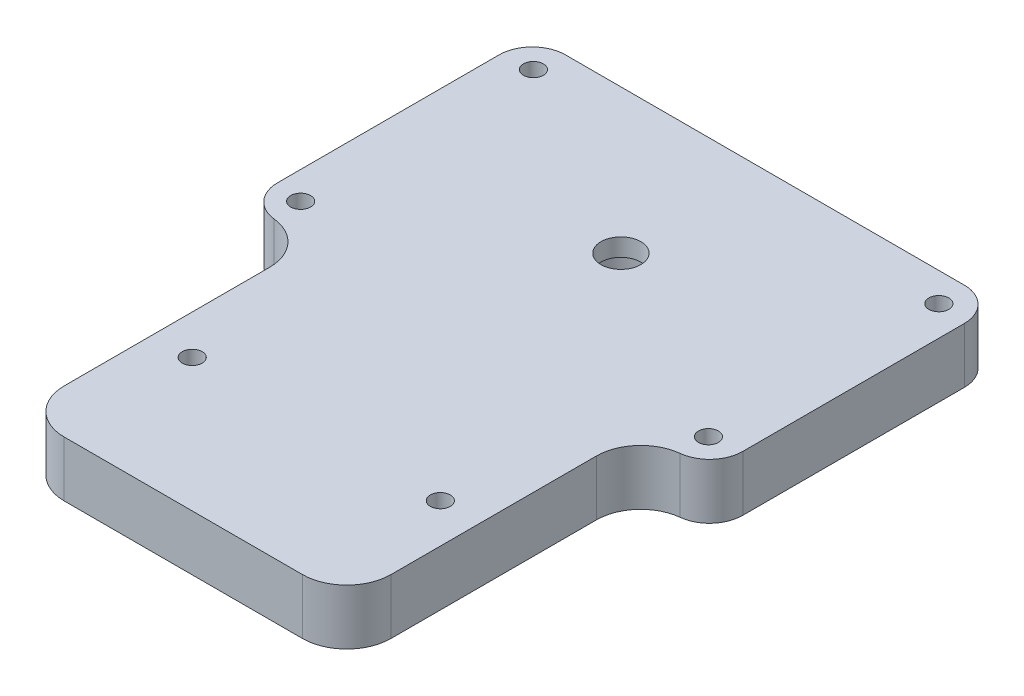
SolidWorks part; units mm, degrees
ref_plane "Front Plane" through (0, 0, 0) normal (0, 0, 1) x (1, 0, 0)
ref_plane "Top Plane" through (0, 0, 0) normal (0, 1, 0) x (1, 0, 0)
ref_plane "Right Plane" through (0, 0, 0) normal (1, 0, 0) x (0, 0, -1)
sketch "Sketch1" plane through (0, 0, 0) normal (0, 1, 0) x (1, 0, 0)
  line L0 (-20.8014, 12.877) -> (26.67, -16.51) construction
  line L1 (-22.86, 16.51) -> (22.86, 16.51)
  line L2 (-26.67, 12.7) -> (-26.67, -12.7)
  line L3 (-22.86, -16.51) -> (-18.7325, -16.51)
  line L4 (26.67, 12.7) -> (26.67, -12.7)
  line L5 (-26.67, 16.51) -> (-22.7451, 14.0803) construction
  line L6 (-26.67, -16.51) -> (26.67, 16.51) construction
  line L7 (18.7325, -16.51) -> (22.86, -16.51)
  line L9 (18.7325, -16.51) -> (18.7325, -50.165)
  line L10 (18.7325, -50.165) -> (-18.7325, -50.165)
  line L11 (-18.7325, -16.51) -> (-18.7325, -50.165)
  circle A0 centre (-23.241, 13.208) radius 1.143
  circle A1 centre (23.241, 13.208) radius 1.143
  circle A2 centre (23.241, -13.208) radius 1.143
  circle A3 centre (-23.5075, -13.208) radius 1.143
  arc A4 (-22.86, 16.51) -> (-26.67, 12.7) centre (-22.86, 12.7) ccw
  arc A5 (-26.67, -12.7) -> (-22.86, -16.51) centre (-22.86, -12.7) ccw
  arc A6 (22.86, -16.51) -> (26.67, -12.7) centre (22.86, -12.7) ccw
  arc A7 (22.86, 16.51) -> (26.67, 12.7) centre (22.86, 12.7) cw
  circle A8 centre (14.224, -34.925) radius 1.143
  circle A9 centre (-14.224, -34.925) radius 1.143
  point P0 (0, 0)
  point P14 (-24.384, 13.208)
  point P18 (24.384, 14.35)
  point P34 (0, -50.165)
  point P39 (13.081, -34.925)
  point P40 (-13.081, -34.925)
  point P41 (14.224, -36.068)
  dimension "D3" = 2.286
  dimension "D5" = 46.482
  dimension "D7" = 26.416
  dimension "D8" = 13.208
  dimension "D9" = 3.81
  dimension "D12" = 2.286
  dimension "D13" = 28.448
  dimension "D14" = 14.224
  dimension "D1" = 53.34
  dimension "D2" = 33.02
  dimension "D4" = 48.768
  dimension "D6" = 23.241
  dimension "D10" = 37.465
  dimension "D11" = 33.655
  dimension "D15" = 15.24
extrude "Boss-Extrude1" add sketch "Sketch1" along normal blind 6.35
sketch "Sketch2" plane through (0, 0, 0) normal (0, -1, 0) x (1, 0, 0)
  circle A0 centre (0, 0) radius 3.81
  dimension "D1" = 7.62
extrude "Cut-Extrude1" cut sketch "Sketch2" against normal blind 4.318
sketch "Sketch3" plane through (0, 4.318, 0) normal (0, -1, 0) x (-1, 0, 0)
  circle A0 centre (0, 0) radius 2.286
  dimension "D1" = 4.572
extrude "Cut-Extrude2" cut sketch "Sketch3" against normal blind 4.318
fillet "Fillet1" radius 5.08 4 edges at (-18.7325, 3.175, 16.51) (18.7325, 3.175, 16.51) (18.7325, 3.175, 50.165) (-18.7325, 3.175, 50.165)
